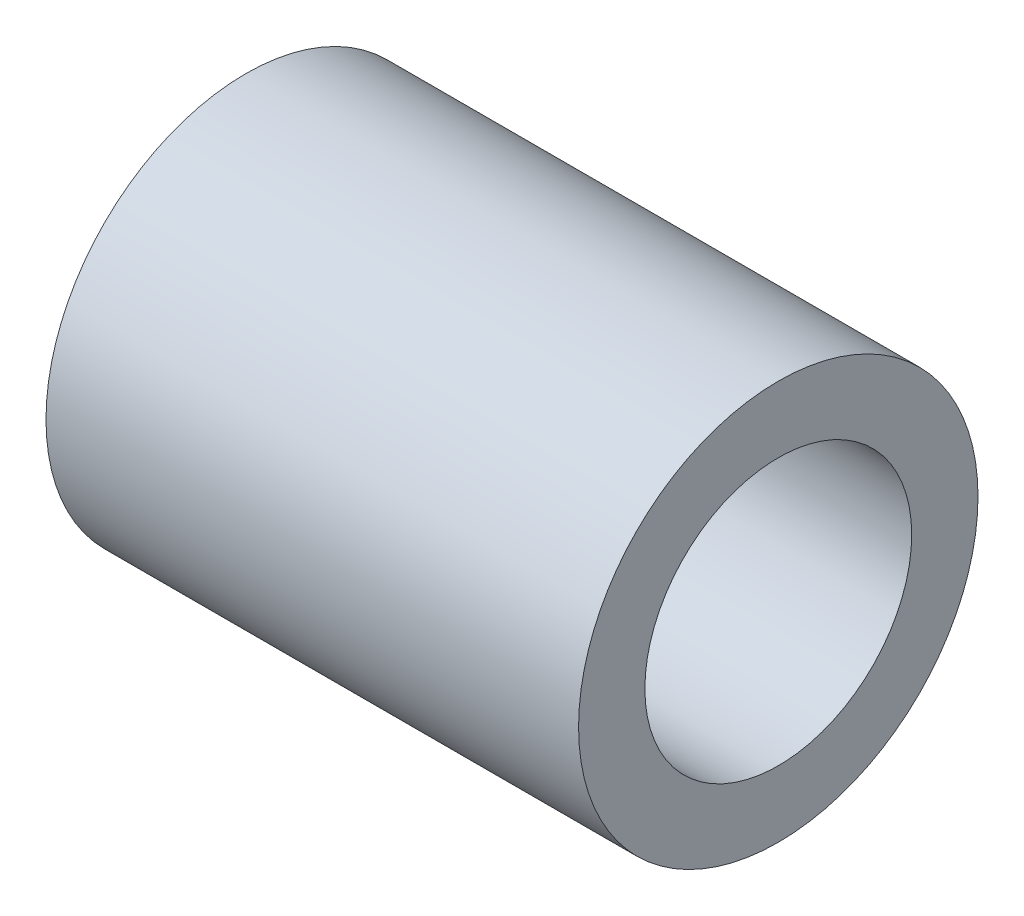
SolidWorks part; units mm, degrees
ref_plane "Front Plane" through (0, 0, 0) normal (0, 0, 1) x (1, 0, 0)
ref_plane "Top Plane" through (0, 0, 0) normal (0, 1, 0) x (1, 0, 0)
ref_plane "Right Plane" through (0, 0, 0) normal (1, 0, 0) x (0, 0, -1)
sketch "Sketch1" plane through (0, 0, 0) normal (1, 0, 0) x (0, 0, -1)
  circle A0 centre (0, 0) radius 6.3627
  circle A1 centre (0, 0) radius 9.525
  dimension "D1" = 12.7254
  dimension "D2" = 19.05
extrude "Boss-Extrude1" add sketch "Sketch1" along normal blind 25.4
